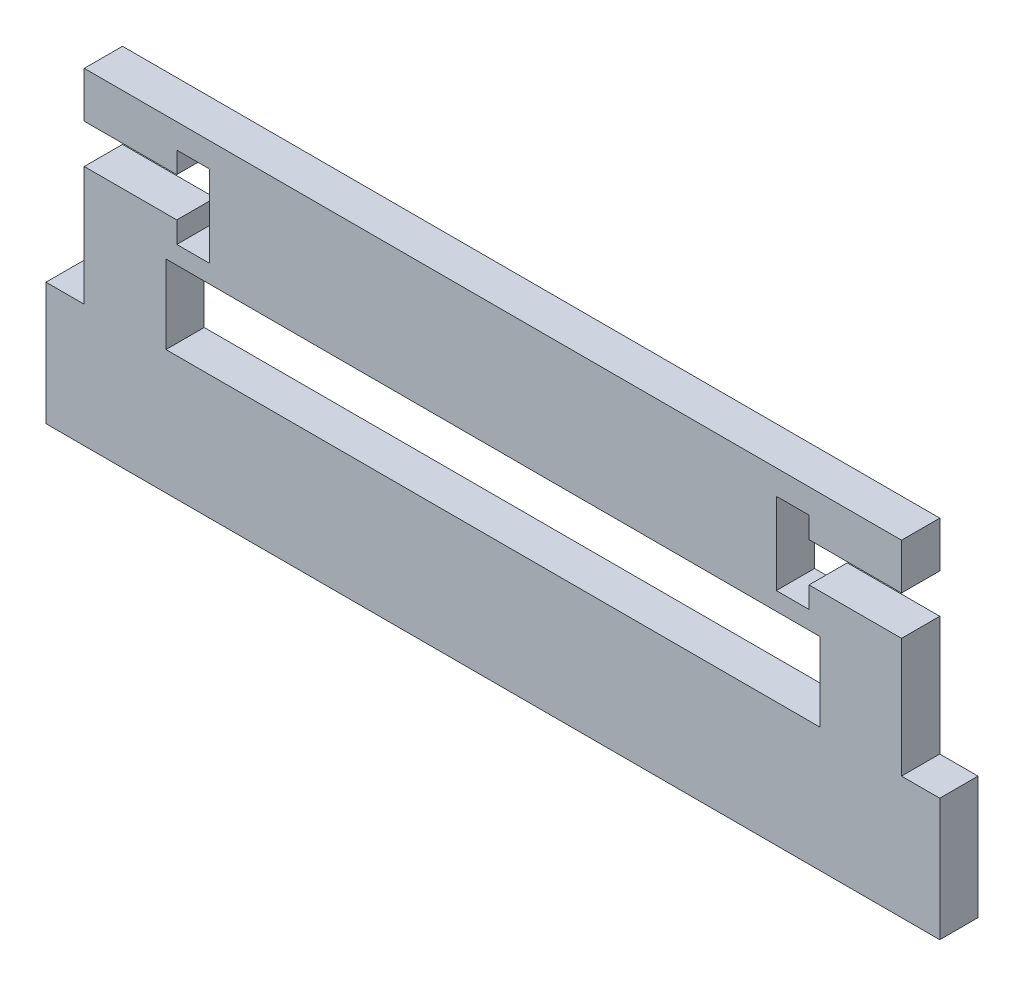
SolidWorks part; units mm, degrees
ref_plane "Front Plane" through (0, 0, 0) normal (0, 0, 1) x (1, 0, 0)
ref_plane "Top Plane" through (0, 0, 0) normal (0, 1, 0) x (1, 0, 0)
ref_plane "Right Plane" through (0, 0, 0) normal (1, 0, 0) x (0, 0, -1)
sketch "Sketch1" plane through (0, 0, 0) normal (0, 0, 1) x (1, 0, 0)
  line L0 (-33.2359, 3.175) -> (-33.2359, -3.175) construction
  line L1 (-31.75, -12.7) -> (31.75, -12.7)
  line L2 (-31.75, -12.7) -> (-31.75, 12.7)
  line L3 (-31.75, 12.7) -> (31.75, 12.7)
  line L4 (31.75, -12.7) -> (31.75, 12.7)
  line L5 (-31.75, 12.7) -> (-34.7218, 12.7)
  line L6 (-31.75, 12.7) -> (-31.75, 3.175)
  line L7 (-31.75, 3.175) -> (-34.7218, 3.175)
  line L8 (-34.7218, 12.7) -> (-34.7218, 3.175)
  line L9 (-31.75, -12.7) -> (-34.7218, -12.7)
  line L10 (-31.75, -12.7) -> (-31.75, -3.175)
  line L11 (-31.75, -3.175) -> (-34.7218, -3.175)
  line L12 (-34.7218, -12.7) -> (-34.7218, -3.175)
  line L13 (0, -55) -> (0, 55) construction
  line L14 (31.75, -3.175) -> (34.7218, -3.175)
  line L15 (34.7218, -12.7) -> (34.7218, -3.175)
  line L16 (31.75, -12.7) -> (34.7218, -12.7)
  line L17 (31.75, -12.7) -> (31.75, -3.175)
  line L18 (31.75, 3.175) -> (34.7218, 3.175)
  line L19 (34.7218, 12.7) -> (34.7218, 3.175)
  line L20 (31.75, 12.7) -> (34.7218, 12.7)
  line L21 (31.75, 12.7) -> (31.75, 3.175)
  line L22 (31.75, 12.7) -> (31.75, 19.05)
  line L23 (-34.7218, 12.7) -> (34.7218, 12.7)
  line L24 (-34.7218, 12.7) -> (-34.7218, 19.05)
  line L25 (-34.7218, 19.05) -> (34.7218, 19.05)
  line L26 (34.7218, 12.7) -> (34.7218, 19.05)
  line L27 (-31.75, 12.7) -> (-31.75, 19.05)
  point P4 (0, 12.7)
  point P6 (31.75, 0)
  point P15 (-33.2359, 0)
  dimension "D1" = 63.5
  dimension "D2" = 25.4
  dimension "D3" = 2.9718
  dimension "D4" = 6.35
  dimension "D5" = 6.35
extrude "Boss-Extrude1" add sketch "Sketch1" along normal blind 2.9718 contours L1 L4 L3 L2 | L12 L9 L2 L11 | L4 L16 L15 L14
sketch "Sketch2" plane through (0, 0, 2.9718) normal (0, 0, 1) x (1, 0, 0)
  line L0 (-34.7218, -12.7) -> (34.7218, -12.7) construction
  line L5 (-25.4, -3.048) -> (25.4, -3.048)
  line L6 (-25.4, -3.048) -> (-25.4, 3.048)
  line L7 (-25.4, 3.048) -> (25.4, 3.048)
  line L8 (25.4, -3.048) -> (25.4, 3.048)
  point P7 (0, 3.048)
  dimension "D1" = 50.8
  dimension "D2" = 9.652
  dimension "D3" = 6.096
extrude "Cut-Extrude1" cut sketch "Sketch2" against normal through all
sketch "Sketch3" plane through (0, 0, 0) normal (0, 0, -1) x (-1, 0, 0)
  line L0 (31.75, 7.62) -> (22.0218, 7.62) construction
  line L1 (31.75, -3.175) -> (31.75, 12.7) construction
  line L2 (22.0218, 10.795) -> (22.0218, 4.445)
  line L3 (34.7218, -12.7) -> (34.7218, -3.175) construction
  line L4 (31.75, 12.7) -> (-31.75, 12.7) construction
  line L5 (31.75, 9.144) -> (24.5618, 9.144)
  line L6 (31.75, 6.096) -> (24.5618, 6.096)
  line L7 (24.5618, 10.795) -> (24.5618, 9.144)
  line L8 (22.0218, 10.795) -> (24.5618, 10.795)
  line L9 (24.5618, 4.445) -> (22.0218, 4.445)
  line L10 (31.75, 9.144) -> (31.75, 6.096)
  line L11 (24.5618, 6.096) -> (24.5618, 4.445)
  line L12 (31.75, 9.144) -> (22.0218, 9.144) construction
  line L13 (0, 55) -> (0, -55) construction
  line L14 (24.5618, 10.795) -> (24.5618, 4.445) construction
  line L15 (31.75, 6.096) -> (22.0218, 6.096) construction
  line L16 (-31.75, 9.144) -> (-31.75, 6.096)
  line L17 (-31.75, 9.144) -> (-24.5618, 9.144)
  line L18 (-24.5618, 10.795) -> (-24.5618, 9.144)
  line L19 (-22.0218, 10.795) -> (-24.5618, 10.795)
  line L20 (-22.0218, 10.795) -> (-22.0218, 4.445)
  line L21 (-24.5618, 4.445) -> (-22.0218, 4.445)
  line L22 (-24.5618, 6.096) -> (-24.5618, 4.445)
  line L23 (-31.75, 6.096) -> (-24.5618, 6.096)
  point P7 (22.0218, 7.62)
  dimension "D1" = 12.7
  dimension "D2" = 6.35
  dimension "D3" = 5.08
  dimension "D4" = 1.524
  dimension "D5" = 1.524
  dimension "D6" = 2.54
extrude "Cut-Extrude2" cut sketch "Sketch3" against normal through all
